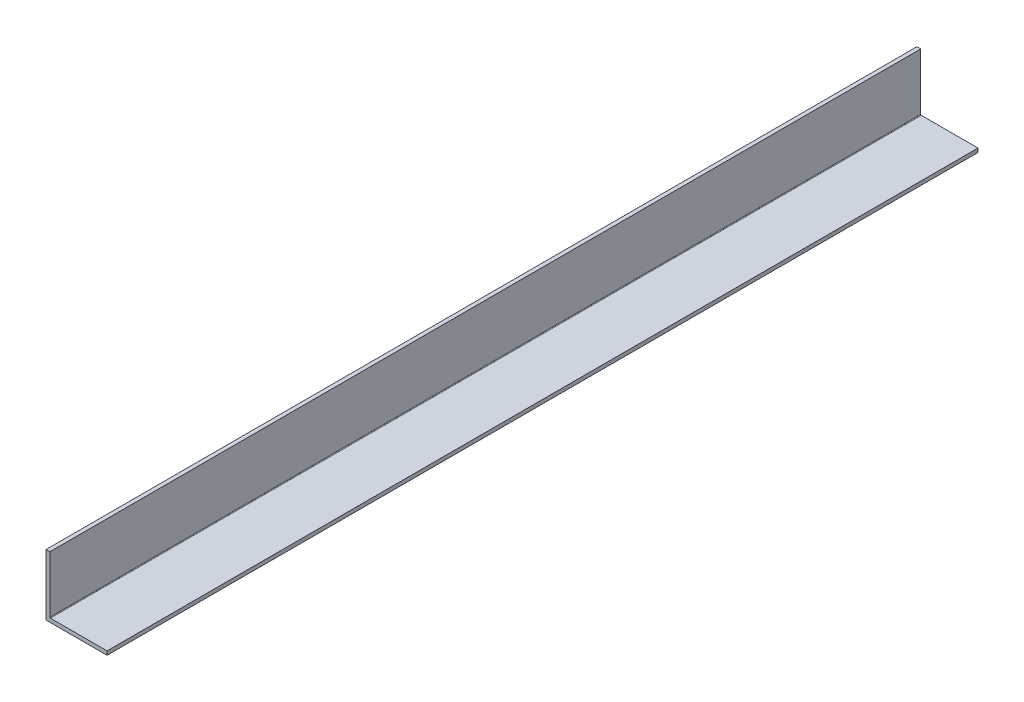
SolidWorks part; units mm, degrees
material "6061-T6 (SS)"
ref_plane "Front Plane" through (0, 0, 0) normal (0, 0, 1) x (1, 0, 0)
ref_plane "Top Plane" through (0, 0, 0) normal (0, 1, 0) x (1, 0, 0)
ref_plane "Right Plane" through (0, 0, 0) normal (1, 0, 0) x (0, 0, -1)
sketch "Sketch1" plane through (0, 0, 0) normal (0, 0, 1) x (1, 0, 0)
  line L0 (0, 25.4) -> (0, 0) construction
  line L1 (0, 0) -> (25.4, 0) construction
  line L2 (25.4, 0) -> (25.4, 1.5875) construction
  line L3 (25.4, 1.5875) -> (1.5875, 1.5875) construction
  line L4 (1.5875, 1.5875) -> (1.5875, 25.4) construction
  line L6 (1.5875, 25.4) -> (0, 25.4) construction
  arc A0 (1.5875, 1.8415) -> (1.8415, 1.5875) centre (1.8415, 1.8415) ccw construction
  point P4 (0, 0)
  dimension "Inside Corner Radius" = 0.254
  dimension "Outside Height" = 25.4
  dimension "Inside Height" = 23.8125
  dimension "Outside Width" = 25.4
  dimension "Inside Width" = 23.8125
  dimension "Wall Thickness" = 1.5875
  dimension "Shape" = 90
sketch "Sketch2" plane through (0, 0, 0) normal (1, 0, 0) x (0, 0, -1)
  line L0 (304.8, 0) -> (-304.8, 0) construction
  line L1 (-304.8, 25.4) -> (-304.8, 0) construction
  line L2 (304.8, 25.4) -> (304.8, 0) construction
  point P0 (-275.59, 0)
  point P4 (0, 0)
  point P6 (275.59, 0)
  dimension "D1" = 29.21
  dimension "D2" = 29.21
  dimension "D3" = 25.4
  dimension "Length" = 609.6
sketch "Sketch3" plane through (0, 0, 0) normal (0, 0, 1) x (1, 0, 0)
  line L0 (1.5875, 25.4) -> (0, 25.4)
  line L1 (0, 25.4) -> (0, 0)
  line L2 (0, 0) -> (25.4, 0)
  line L3 (25.4, 0) -> (25.4, 1.5875)
  line L4 (25.4, 1.5875) -> (1.5875, 1.5875)
  line L5 (1.5875, 1.5875) -> (1.5875, 25.4)
extrude "Boss-Extrude1" add sketch "Sketch3" along normal mid plane 609.6
fillet "Fillet1" radius 0.254 1 edges at (1.5875, 1.5875, 0)
sketch "Sketch4" plane through (0, 0, -304.8) normal (0, 0, -1) x (-1, 0, 0)
  line L6 (-1.5875, 25.4) -> (-1.5875, 1.8415)
  line L7 (-1.8415, 1.5875) -> (-25.4, 1.5875)
  line L8 (-25.4, 1.5875) -> (-25.4, 0)
  line L9 (-25.4, 0) -> (0, 0)
  line L10 (0, 0) -> (0, 25.4)
  line L11 (0, 25.4) -> (-1.5875, 25.4)
  line L12 (-1.5875, 25.4) -> (-1.5875, 1.8415)
  line L13 (-1.8415, 1.5875) -> (-25.4, 1.5875)
  line L14 (-25.4, 1.5875) -> (-25.4, 0)
  line L15 (-25.4, 0) -> (0, 0)
  line L16 (0, 0) -> (0, 25.4)
  line L17 (0, 25.4) -> (-1.5875, 25.4)
  arc A1 (-1.8415, 1.5875) -> (-1.5875, 1.8415) centre (-1.8415, 1.8415) ccw
  arc A2 (-1.8415, 1.5875) -> (-1.5875, 1.8415) centre (-1.8415, 1.8415) ccw
  dimension "D1" = 0
extrude "Cut-Extrude1" cut sketch "Sketch4" against normal offset from surface (247.35 mm away) 362.25 up to face at (7.9663, 7.9663, 304.8)
equation "\"D1@Boss-Extrude1\"=\"Length@Sketch2\""
equation "\"D1@Sketch2\" = \"Outside Width@Sketch1\" * 1.15"
equation "\"D2@Sketch2\"=\"D1@Sketch2\""
equation "\"D1@Fillet1\"=\"Inside Corner Radius@Sketch1\""
equation "\"D3@Sketch2\"=\"Outside Height@Sketch1\""
